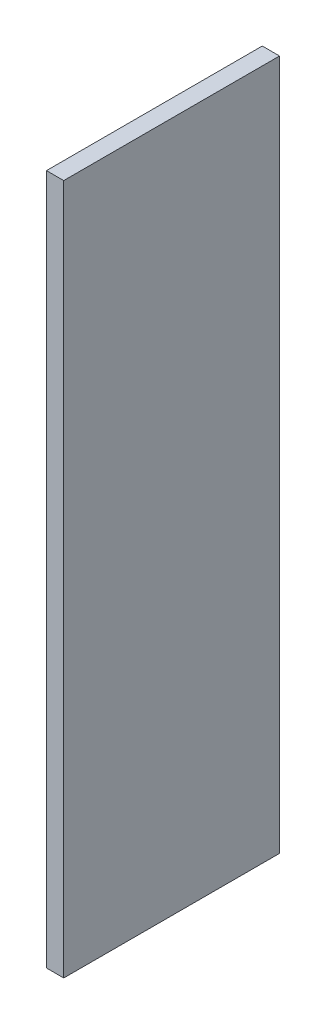
SolidWorks part; units mm, degrees
ref_plane "Front" through (0, 0, 0) normal (0, 0, 1) x (1, 0, 0)
ref_plane "Top" through (0, 0, 0) normal (0, 1, 0) x (1, 0, 0)
ref_plane "Right" through (0, 0, 0) normal (1, 0, 0) x (0, 0, -1)
sketch "Sketch1" plane through (0, 0, 0) normal (0, 1, 0) x (1, 0, 0)
  line L1 (0, 0) -> (2.54, 0)
  line L2 (0, 0) -> (0, 31.75)
  line L3 (0, 31.75) -> (2.54, 31.75)
  line L4 (2.54, 0) -> (2.54, 31.75)
  line L5 (0, 0) -> (2.54, 31.75) construction
  line L6 (0, 31.75) -> (2.54, 0) construction
  point P4 (1.27, 15.875)
  dimension "D1" = 31.75
  dimension "D2" = 2.54
extrude "Boss-Extrude1" add sketch "Sketch1" along normal blind 101.6
sketch "Sketch5" plane through (0, 0, 0) normal (1, 0, 0) x (0, 0, -1)
  line L0 (15.875, 0) -> (15.875, 19.05) construction
  line L1 (31.75, 0) -> (0, 0) construction
  line L2 (31.75, 51.2169) -> (0.4972, 51.2169) construction
  line L3 (31.75, 101.6) -> (31.75, 0) construction
  circle A0 centre (15.875, 19.05) radius 4.7625
  circle A1 centre (15.875, 19.05) radius 3.175
  circle A2 centre (15.875, 83.3838) radius 3.175
  circle A3 centre (15.875, 83.3838) radius 4.7625
  dimension "D2" = 9.525
  dimension "D3" = 6.35
  dimension "D1" = 19.05
extrude "Boss-Extrude3" add sketch "Sketch5" against normal blind 6.35
